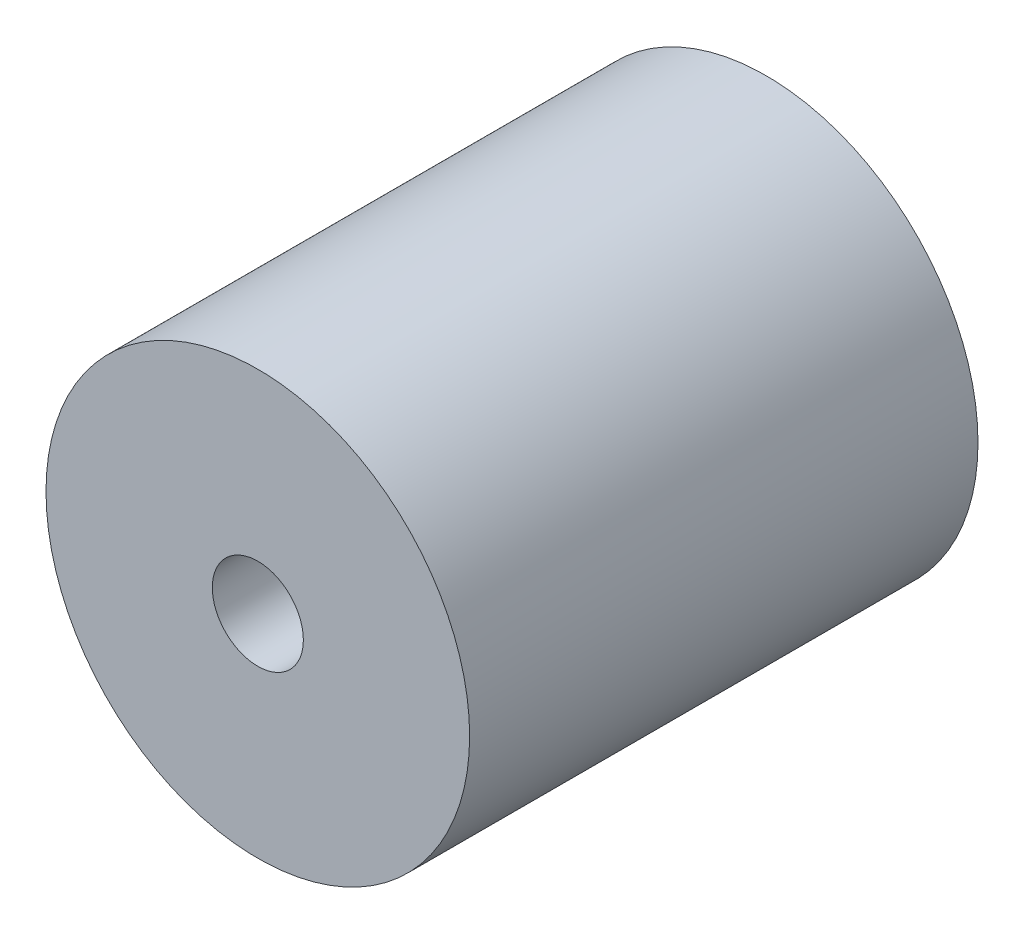
SolidWorks part; units mm, degrees
material "Balsa"
ref_plane "前视基准面" through (0, 0, 0) normal (0, 0, 1) x (1, 0, 0)
ref_plane "上视基准面" through (0, 0, 0) normal (0, 1, 0) x (1, 0, 0)
ref_plane "右视基准面" through (0, 0, 0) normal (1, 0, 0) x (0, 0, -1)
other "Configuration Table"
sketch "Sketch1" plane through (0, 0, 0) normal (0, 0, 1) x (1, 0, 0)
  circle A0 centre (0, 0) radius 10
  circle A1 centre (0, 0) radius 2.15
  dimension "D1" = 20
  dimension "D2" = 4.3
extrude "Boss-Extrude1" add sketch "Sketch1" along normal blind 24
